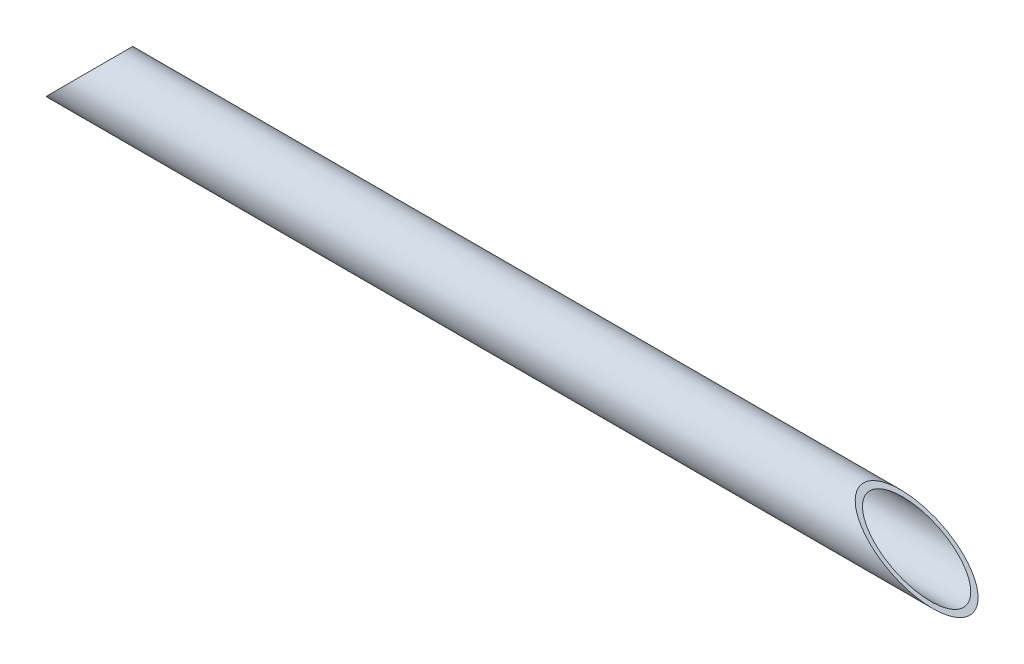
SolidWorks part; units mm, degrees
material "1.4301 (X5CrNi18-10)"
ref_plane "Front" through (0, 0, 0) normal (0, 0, 1) x (1, 0, 0)
ref_plane "Top" through (0, 0, 0) normal (0, 1, 0) x (1, 0, 0)
ref_plane "Right" through (0, 0, 0) normal (1, 0, 0) x (0, 0, -1)
sketch "Skizze1" plane through (0, 0, 0) normal (0, 0, 1) x (1, 0, 0)
  line L0 (0, 0) -> (500, 0)
  dimension "D1" = 500
other "Rohr 33.7 X 2.0(1)"
ref_plane "Ebene1" through (0, 0, 0) normal (1, 0, 0) x (0, 1, 0)
sketch "Sketch1" plane through (0, 0, 0) normal (1, 0, 0) x (0, 1, 0)
  circle A0 centre (0, 0) radius 14.85
  circle A1 centre (0, 0) radius 16.85
  point P3 (0, 0)
  dimension "In_dia" = 29.7
  dimension "Out_dia" = 33.7
sketch "Skizze3" plane through (0, 0, 0) normal (0, 0, 1) x (1, 0, 0)
  line L0 (0, -16.85) -> (122.8029, 105.9529)
  line L1 (122.8029, 105.9529) -> (287.2992, 105.9529)
  line L2 (287.2992, 105.9529) -> (500, -16.85)
  dimension "D1" = 135
  dimension "D2" = 30
extrude "Winkel" cut sketch "Skizze3" against normal through all both and the other way through all
